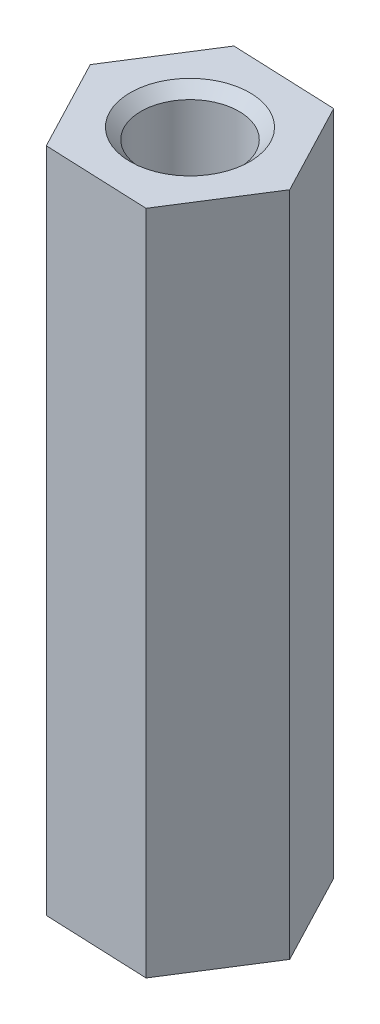
SolidWorks part; units mm, degrees
ref_plane "前视基准面" through (0, 0, 0) normal (0, 0, 1) x (1, 0, 0)
ref_plane "上视基准面" through (0, 0, 0) normal (0, 1, 0) x (1, 0, 0)
ref_plane "右视基准面" through (0, 0, 0) normal (1, 0, 0) x (0, 0, -1)
sketch "草图1" plane through (0, 0, 0) normal (0, 1, 0) x (1, 0, 0)
  line L1 (1.2317, -2.3529) -> (2.6535, -0.1098)
  line L2 (2.6535, -0.1098) -> (1.4218, 2.2432)
  line L3 (1.4218, 2.2432) -> (-1.2317, 2.3529)
  line L4 (-1.2317, 2.3529) -> (-2.6535, 0.1098)
  line L5 (-2.6535, 0.1098) -> (-1.4218, -2.2432)
  line L6 (-1.4218, -2.2432) -> (1.2317, -2.3529)
  circle A0 centre (0, 0) radius 2.3 construction
  circle A1 centre (0, 0) radius 1.1
  dimension "D2" = 2.2
  dimension "D1" = 4.6
extrude "凸台-拉伸1" add sketch "草图1" along normal blind 17
hole_wizard "M3 螺纹孔2" positions "草图2" profile "草图3" tap size "M3" standard "GB" end condition through all
sketch "草图2" plane through (0, 17, 0) normal (0, 1, 0) x (1, 0, 0)
  point P0 (0, 0)
sketch "草图3" plane through (0, 17, 0) normal (1, 0, 0) x (0, 0, 1)
  line L0 (0, 0) -> (0, 17)
  line L1 (0, 17) -> (1.25, 17)
  line L2 (1.25, 17) -> (1.25, 0.275)
  line L3 (1.25, 0.275) -> (1.525, 0)
  line L5 (1.525, 0) -> (0, 0)
  line L6 (-1.25, 0.275) -> (-1.525, 0) construction
  line L11 (0, -6.35) -> (0, 107.95) construction
  dimension "通孔螺纹孔钻头直径" = 2.5
  dimension "通孔螺纹孔钻头深度" = 17
  dimension "近端锥形沉头孔直径" = 3.05
  dimension "近端锥形沉头孔角度" = 90
cosmetic thread "孔螺蚊线2" parameters "D2"=3
